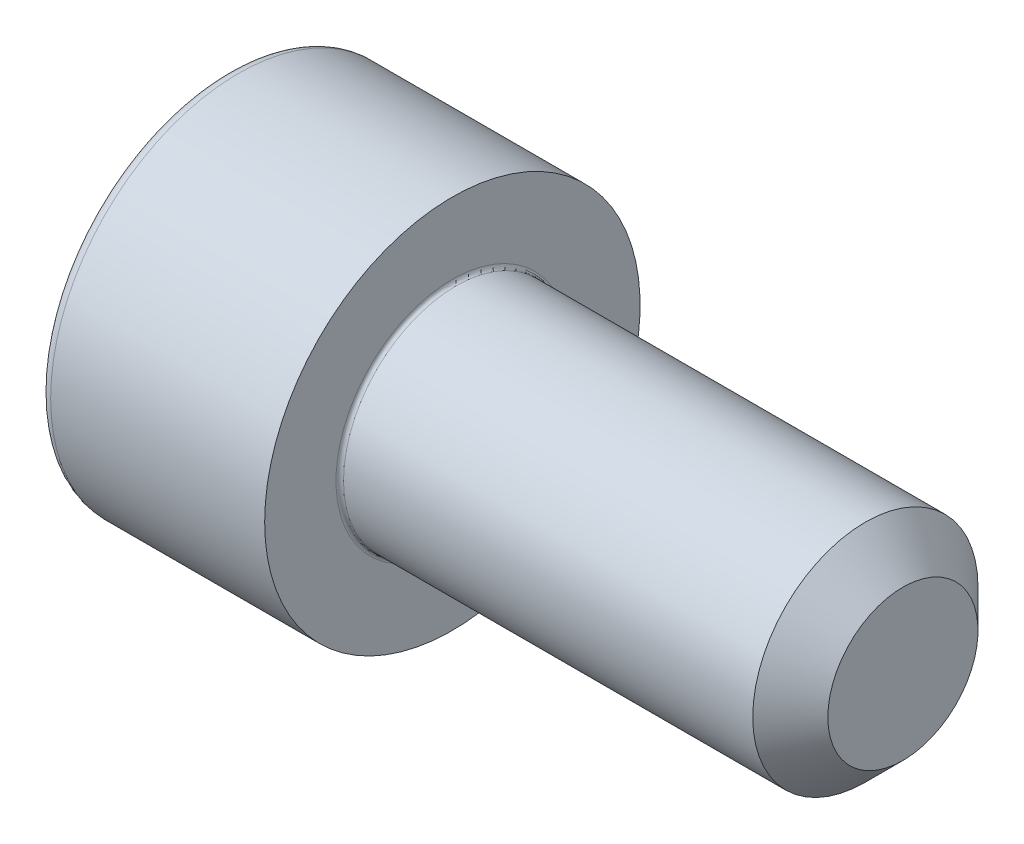
SolidWorks part; units mm, degrees
revolve "Base-Revolve" add sketch "BodySke"
sketch "BodySke" plane through (0, 0, 0) normal (0, 0, 1) x (1, 0, 0)
  line L0 (0, 0) -> (0, 5)
  line L1 (0, 5) -> (6, 5)
  line L2 (6, 5) -> (6, 3)
  line L3 (6, 3) -> (17, 3)
  line L4 (18, 2) -> (18, 0)
  line L5 (18, 0) -> (0, 0)
  line L6 (-31.75, 0) -> (127, 0) construction
  line L8 (18, 2) -> (17, 3)
  line L10 (18, -2) -> (17, -3) construction
  line L11 (6.5, 9.525) -> (6.5, 3.175) construction
  line L12 (6, 9.525) -> (6, 3.175) construction
  line L13 (2.0069, 9.525) -> (2.0069, 3.175) construction
  dimension "Head_ht" = 6
  dimension "Length" = 12
  dimension "Body_ch_ang" = 45
  dimension "Diameter" = 6
  dimension "Minor_dia" = 4
  dimension "Advance" = 0.5
  dimension "Thread_nom" = 12
  dimension "Thread_length" = 15.9931
  dimension "Head_dia" = 10
cosmetic thread "ThreadCosmetic" [suppressed]
fillet "Fillet1" radius 0.1 1 edges at (6, 0, 3)
fillet "Fillet2" radius 0.3 1 edges at (0, 0, 5)
ref_plane "Plane1" through (0, 0, 0) normal (0, 0, 1) x (1, 0, 0)
ref_plane "Plane2" through (0, 0, 0) normal (0, 1, 0) x (1, 0, 0)
ref_plane "Plane3" through (0, 0, 0) normal (1, 0, 0) x (0, 0, -1)
sketch "Sketch2" plane through (0, 0, 0) normal (0, 0, 1) x (1, 0, 0)
  line L0 (0, 2.5) -> (1.3, 2.5)
  line L1 (1.3, 2.5) -> (2.7434, 0)
  line L2 (-31.75, 0) -> (127, 0) construction
  line L3 (2.7434, 0) -> (0, 0)
  line L4 (0, 0) -> (0, 2.5)
  line L6 (0, 0) -> (47.625, 0) construction
  dimension "D1" = 2.5
  dimension "D2" = 60
  dimension "Depth" = 1.3
revolve "Hex-PreBroach" cut sketch "Sketch2" angle 360 about L6
sketch "Sketch3" plane through (0, 0, 0) normal (-1, 0, 0) x (0, 0.5, 0.866)
  line L0 (1.4434, 2.5) -> (-1.4434, 2.5)
  line L1 (-1.4434, 2.5) -> (-2.8868, 0)
  line L2 (1.4434, 2.5) -> (2.8868, 0)
  line L3 (1.4434, -2.5) -> (2.8868, 0)
  line L4 (1.4434, -2.5) -> (-1.4434, -2.5)
  line L5 (-1.4434, -2.5) -> (-2.8868, 0)
  dimension "D1" = 2.5
  dimension "D2" = 2.5
  dimension "Hex_size" = 5
extrude "Hex" cut sketch "Sketch3" against normal blind 1.3
sketch "ThdSchSke" plane through (0, 0, 0) normal (0, 0, 1) x (1, 0, 0)
  line L0 (7.5, -2) -> (6.7998, -3)
  line L1 (7.5, -2) -> (8.2002, -3)
  line L2 (8.2002, -3) -> (8.2002, -3.75)
  line L3 (-3.175, 0) -> (5.1513, 0) construction
  line L4 (0, 4.7) -> (0, -4.7) construction
  line L5 (8.2002, -3.75) -> (6.7998, -3.75)
  line L6 (6.7998, -3.75) -> (6.7998, -3)
  dimension "Thread_minor" = 4
  dimension "Diameter" = 6
  dimension "Start" = 7.5
revolve "ThreadSchematic" [suppressed] cut sketch "ThdSchSke" angle 360 about L3
pattern_linear "ThdSchPat" [suppressed]
equation "\"D2@Sketch3\" = \"Hex_size@Sketch3\" / 2"
equation "\"D1@Sketch3\" = \"Hex_size@Sketch3\" / 2"
equation "\"D1@Sketch2\" = \"Hex_size@Sketch3\" / 2"
equation "\"Thread_minor@ThreadCosmetic\"  =  \"Minor_dia@BodySke\""
equation "\"Depth@Sketch2\" =  \"Key_eng@Hex\""
equation "\"Thread_length@ThreadCosmetic\" = ((sgn( (\"Length@BodySke\" - \"Advance@BodySke\" * 3.0) - \"Thread_nom@BodySke\" )-1)*( (\"Length@BodySke\" - \"Advance@BodySke\" * 3.0) - \"Thread_nom@BodySke\" ))/-2+ \"Thread_nom@BodySke\""
equation "\"Thread_minor@ThdSchSke\" = \"Minor_dia@BodySke\""
equation "\"Diameter@ThdSchSke\" = \"Diameter@BodySke\""
equation "\"Overcut@ThdSchSke\" = \"Diameter@BodySke\" * 1.25"
equation "\"Start@ThdSchSke\" = \"Head_ht@BodySke\" + \"Length@BodySke\" - \"Thread_length@ThreadCosmetic\"  '---Non-countersunk---"
equation "\"Num_threads@ThdSchPat\" = int( \"Thread_length@ThreadCosmetic\" / \"Advance@BodySke\" + 0.999 )  + 1"
equation "\"Advance@ThdSchPat\" = \"Thread_length@ThreadCosmetic\" /  (\"Num_threads@ThdSchPat\" - 1) 'relax it"
equation "\"Num_threads@ThdSchPat\" = \"Num_threads@ThdSchPat\" - sgn( \"Num_threads@ThdSchPat\" - 1) '---chamfered tips only---"
